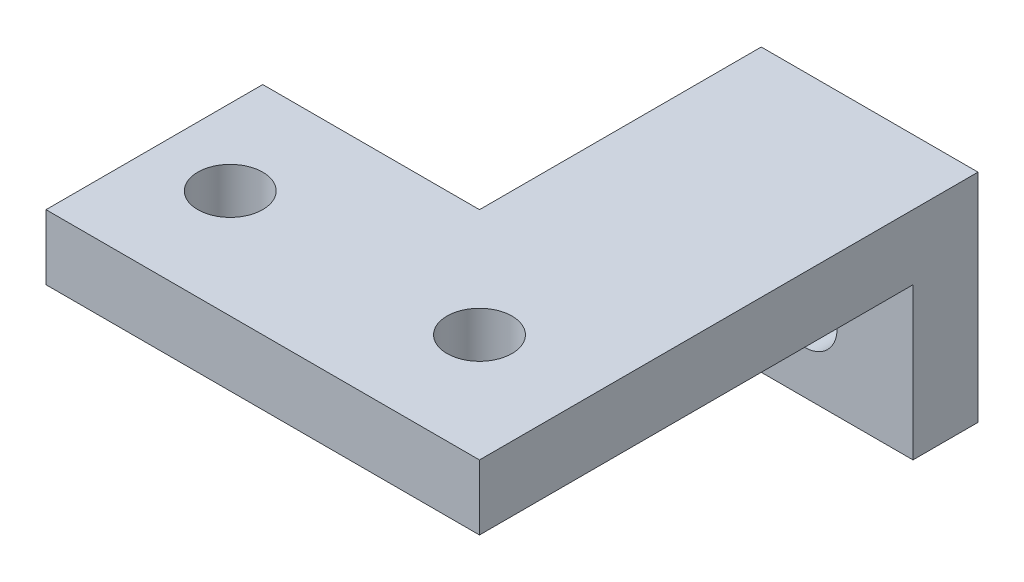
SolidWorks part; units mm, degrees
ref_plane "Front Plane" through (0, 0, 0) normal (0, 0, 1) x (1, 0, 0)
ref_plane "Top Plane" through (0, 0, 0) normal (0, 1, 0) x (1, 0, 0)
ref_plane "Right Plane" through (0, 0, 0) normal (1, 0, 0) x (0, 0, -1)
sketch "Sketch1" plane through (0, 0, 0) normal (0, 1, 0) x (1, 0, 0)
  line L0 (0, 0) -> (20, 0)
  line L1 (20, 0) -> (20, 23)
  line L2 (20, 23) -> (10, 23)
  line L3 (10, 23) -> (10, 10)
  line L4 (10, 10) -> (0, 10)
  line L5 (0, 10) -> (0, 0)
  dimension "D1" = 20
  dimension "D2" = 23
  dimension "D3" = 10
  dimension "D4" = 10
extrude "Boss-Extrude1" add sketch "Sketch1" along normal blind 3 contours L3 L4 L5 L0 L1 L2
sketch "Sketch7" plane through (0, 0, 0) normal (0, -1, 0) x (1, 0, 0)
  line L0 (10, -23) -> (10, -10) construction
  line L1 (10, -20) -> (20, -20)
  line L2 (10, -20) -> (10, -23)
  line L3 (10, -23) -> (20, -23)
  line L4 (20, -20) -> (20, -23)
  line L5 (10, -20) -> (20, -23) construction
  line L6 (10, -23) -> (20, -20) construction
  point P0 (15, -21.5)
  dimension "D1" = 3
extrude "Boss-Extrude2" add sketch "Sketch7" along normal blind 7
sketch "Sketch8" plane through (0, 0, -23) normal (0, 0, -1) x (-1, 0, 0)
  line L0 (-10, -7) -> (-20, -7) construction
  circle A0 centre (-15, -3.5) radius 1.5
  dimension "D1" = 3
  dimension "D2" = 3.5
  dimension "D3" = 5
extrude "Cut-Extrude1" cut sketch "Sketch8" against normal up to next
sketch "Sketch12" plane through (0, 3, 0) normal (0, 1, 0) x (1, 0, 0)
  circle A0 centre (15, 5) radius 1.5
  circle A1 centre (3.5, 5) radius 1.5
  dimension "D1" = 3
  dimension "D2" = 5
  dimension "D3" = 5
  dimension "D4" = 3.5
  dimension "D5" = 5
extrude "Cut-Extrude2" cut sketch "Sketch12" against normal up to next
